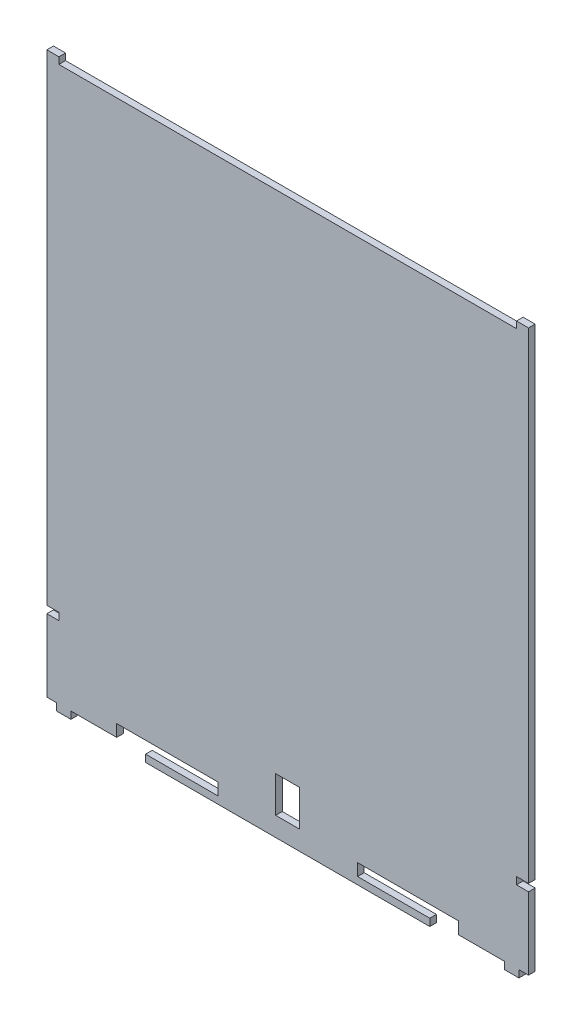
SolidWorks part; units mm, degrees
ref_plane "前视基准面" through (0, 0, 0) normal (0, 0, 1) x (1, 0, 0)
ref_plane "上视基准面" through (0, 0, 0) normal (0, 1, 0) x (1, 0, 0)
ref_plane "右视基准面" through (0, 0, 0) normal (1, 0, 0) x (0, 0, -1)
sketch "草图1" plane through (0, 0, 0) normal (0, 0, 1) x (1, 0, 0)
  line L0 (0, 0) -> (4, 0)
  line L1 (0, 0) -> (4, 0)
  line L2 (0, 0) -> (0, 27)
  line L4 (200, 0) -> (200, 27)
  line L5 (0, 30) -> (5, 30)
  line L6 (0, 33) -> (0, 230)
  line L7 (5, 230) -> (195, 230)
  line L8 (200, 33) -> (200, 230)
  line L9 (4, 0) -> (4, -3)
  line L10 (4, -3) -> (10, -3)
  line L11 (10, -3) -> (10, 0)
  line L12 (200, 0) -> (196, 0)
  line L13 (196, 0) -> (196, -3)
  line L14 (196, -3) -> (190, -3)
  line L15 (190, -3) -> (190, 0)
  line L16 (0, 0) -> (4, 0)
  line L17 (29, 0) -> (29, 5)
  line L18 (200, 0) -> (196, 0)
  line L19 (29, 5) -> (71, 5)
  line L20 (159, -3) -> (41, -3)
  line L21 (171, 0) -> (190, 0)
  line L22 (0, 0) -> (4, 0)
  line L23 (41, 0) -> (41, -3)
  line L24 (200, 0) -> (196, 0)
  line L25 (159, 0) -> (159, -3)
  line L26 (71, 5) -> (71, 0)
  line L27 (71, 0) -> (41, 0)
  line L28 (171, 0) -> (171, 5)
  line L29 (171, 5) -> (129, 5)
  line L30 (129, 5) -> (129, 0)
  line L31 (129, 0) -> (159, 0)
  line L32 (0, 30) -> (5, 30)
  line L35 (200, 30) -> (195, 30)
  line L36 (5, 30) -> (5, 33)
  line L37 (5, 33) -> (0, 33)
  line L38 (195, 30) -> (200, 30)
  line L39 (200, 33) -> (200, 230)
  line L40 (190, 0) -> (171, 0)
  line L41 (196, 0) -> (200, 0)
  line L42 (190, 0) -> (159, 0)
  line L43 (10, 0) -> (29, 0)
  line L44 (10, 0) -> (29, 0)
  line L45 (10, 0) -> (41, 0)
  line L46 (0, 230) -> (0, 232.75)
  line L47 (0, 232.75) -> (5, 232.75)
  line L48 (5, 232.75) -> (5, 230)
  line L49 (200, 230) -> (200, 232.75)
  line L50 (200, 232.75) -> (195, 232.75)
  line L51 (195, 232.75) -> (195, 230)
  line L52 (0, 30) -> (0, 27)
  line L54 (100, 5) -> (105, 5)
  line L55 (105, 5) -> (105, 20)
  line L56 (105, 20) -> (95, 20)
  line L57 (95, 20) -> (95, 5)
  line L58 (95, 5) -> (100, 5)
  line L59 (195, 30) -> (195, 33)
  line L60 (195, 33) -> (200, 33)
  line L61 (200, 27) -> (200, 30)
extrude "凸台-拉伸1" add sketch "草图1" along normal blind 2.75 contours L4 L61 L35 L59 L60 L8 L49 L50 L51 L7 L48 L47 L46 L6 L37 L36 L5 L52 L2 L0 L9 L10 L11 L43 L17 L19 L26 L27 L23 L20 L25 L31 L30 L29 L28 L21 L15 L14 L13 L12 L58 L57 L56 L55 L54
